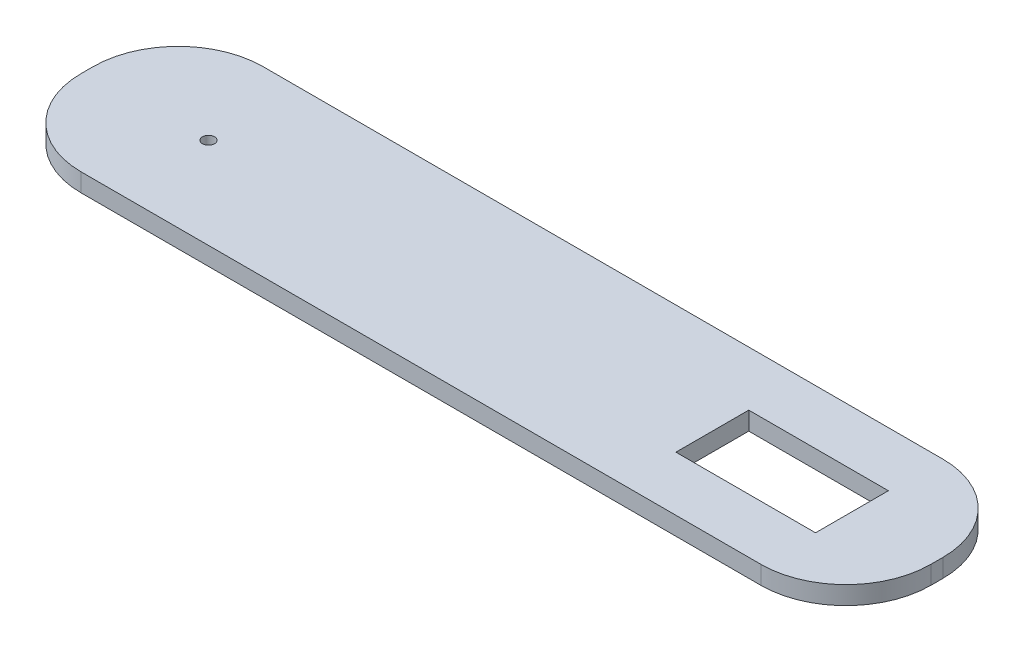
SolidWorks part; units mm, degrees
ref_plane "Front Plane" through (0, 0, 0) normal (0, 0, 1) x (1, 0, 0)
ref_plane "Top Plane" through (0, 0, 0) normal (0, 1, 0) x (1, 0, 0)
ref_plane "Right Plane" through (0, 0, 0) normal (1, 0, 0) x (0, 0, -1)
sketch "Sketch1" plane through (0, 0, 0) normal (0, 1, 0) x (1, 0, 0)
  line L1 (0, 0) -> (140, 0)
  line L2 (0, 0) -> (0, 30)
  line L3 (0, 30) -> (140, 30)
  line L4 (140, 0) -> (140, 30)
  dimension "D1" = 30
  dimension "D2" = 140
extrude "Boss-Extrude1" add sketch "Sketch1" along normal blind 3
sketch "Sketch2" plane through (0, 3, 0) normal (0, 1, 0) x (1, 0, 0)
  line L0 (0, 30) -> (0, 0) construction
  line L1 (140, 30) -> (0, 30) construction
  line L2 (0, 0) -> (140, 0) construction
  line L3 (103, 21) -> (126, 21)
  line L4 (103, 21) -> (103, 9)
  line L5 (103, 9) -> (126, 9)
  line L6 (126, 21) -> (126, 9)
  line L7 (140, 0) -> (140, 30) construction
  circle A0 centre (20, 15) radius 1
  dimension "D1" = 2
  dimension "D3" = 15
  dimension "D2" = 20
  dimension "D4" = 23
  dimension "D5" = 12
  dimension "D6" = 9
  dimension "D7" = 14
extrude "Cut-Extrude1" cut sketch "Sketch2" against normal through all
fillet "Fillet1" radius 14 4 edges at (140, 1.5, -30) (140, 1.5, 0) (0, 1.5, -30) (0, 1.5, 0)
